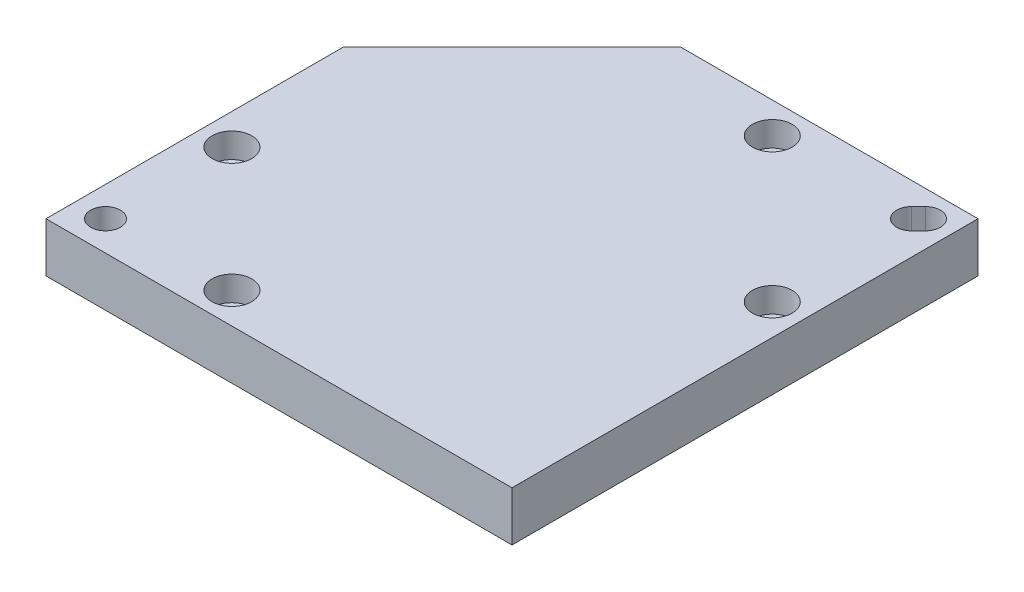
SolidWorks part; units mm, degrees
ref_plane "Front Plane" through (0, 0, 0) normal (0, 0, 1) x (1, 0, 0)
ref_plane "Top Plane" through (0, 0, 0) normal (0, 1, 0) x (1, 0, 0)
ref_plane "Right Plane" through (0, 0, 0) normal (1, 0, 0) x (0, 0, -1)
sketch "Sketch2" plane through (0, 0, 0) normal (0, 1, 0) x (1, 0, 0)
  line L0 (0, -34) -> (34, 0)
  line L1 (34, 0) -> (94, 0)
  line L2 (0, -34) -> (0, -94)
  line L3 (0, -94) -> (94, -94)
  line L4 (94, 0) -> (94, -94)
  dimension "D1" = 94
  dimension "D2" = 94
  dimension "D3" = 60
  dimension "D4" = 60
extrude "Boss-Extrude1" add sketch "Sketch2" along normal blind 10
sketch "Sketch3" plane through (0, 10, 0) normal (0, 1, 0) x (1, 0, 0)
  line L0 (94, 0) -> (34, 0) construction
  line L1 (94, -94) -> (94, 0) construction
  line L2 (0, -94) -> (94, -94) construction
  line L3 (0, -34) -> (0, -94) construction
  line L4 (88.7071, -5.2929) -> (87.2929, -6.7071) construction
  line L5 (90.8284, -7.4142) -> (89.4142, -8.8284)
  line L6 (86.5858, -3.1716) -> (85.1716, -4.5858)
  line L7 (94, 0) -> (84.2929, -9.7071) construction
  circle A0 centre (58.75, -6.25) radius 2.25
  circle A1 centre (87.75, -35.25) radius 2.25
  circle A2 centre (6.25, -62.75) radius 2.25
  circle A3 centre (31.25, -87.75) radius 2.25
  circle A4 centre (6, -88) radius 3
  arc A5 (90.8284, -7.4142) -> (86.5858, -3.1716) centre (88.7071, -5.2929) ccw
  arc A6 (85.1716, -4.5858) -> (89.4142, -8.8284) centre (87.2929, -6.7071) ccw
  point P20 (88, -6)
  point P25 (85.8787, -3.8787)
  point P29 (0, 0)
  point P30 (84.2929, -9.7071)
  point P31 (0, 0)
  dimension "D1" = 4.5
  dimension "D2" = 6.25
  dimension "D10" = 6
  dimension "D3" = 35.25
  dimension "D4" = 6.25
  dimension "D5" = 35.25
  dimension "D6" = 6.25
  dimension "D7" = 6.25
  dimension "D8" = 31.25
  dimension "D9" = 31.25
  dimension "D11" = 6
  dimension "D12" = 6
  dimension "D13" = 6
  dimension "D14" = 2
  dimension "D15" = 6
  dimension "D16" = 6
extrude "Cut-Extrude1" cut sketch "Sketch3" against normal blind 10
sketch "Sketch5" plane through (0, 10, 0) normal (0, 1, 0) x (1, 0, 0)
  circle A0 centre (58.75, -6.25) radius 4
  circle A1 centre (87.75, -35.25) radius 4
  circle A2 centre (6.25, -62.75) radius 4
  circle A3 centre (31.25, -87.75) radius 4
  dimension "D1" = 8
extrude "Cut-Extrude2" cut sketch "Sketch5" against normal blind 5
